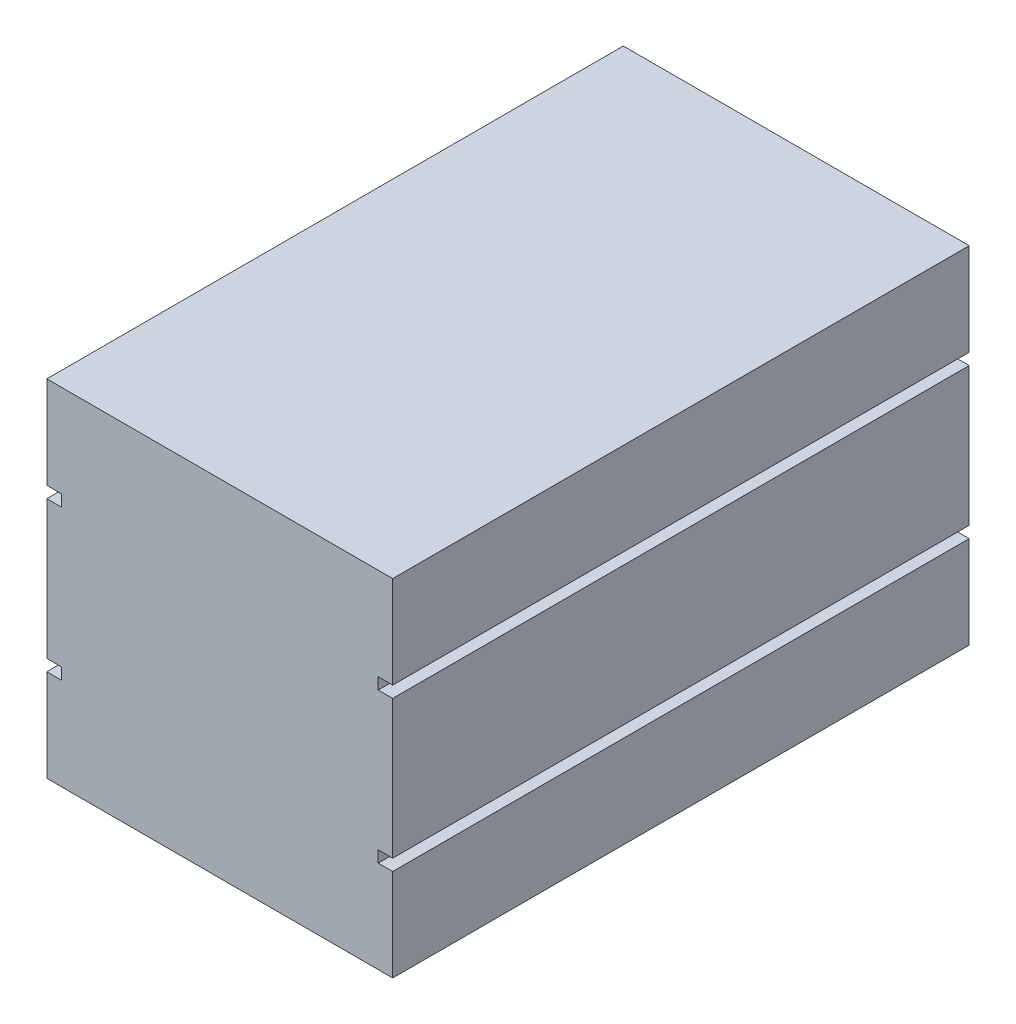
SolidWorks part; units mm, degrees
ref_plane "Front Plane" through (0, 0, 0) normal (0, 0, 1) x (1, 0, 0)
ref_plane "Top Plane" through (0, 0, 0) normal (0, 1, 0) x (1, 0, 0)
ref_plane "Right Plane" through (0, 0, 0) normal (1, 0, 0) x (0, 0, -1)
sketch "Sketch1" plane through (0, 0, 0) normal (1, 0, 0) x (0, 0, -1)
  line L1 (-25, -15) -> (25, -15)
  line L2 (-25, -15) -> (-25, 15)
  line L3 (-25, 15) -> (25, 15)
  line L4 (25, -15) -> (25, 15)
  line L5 (-25, -15) -> (25, 15) construction
  line L6 (-25, 15) -> (25, -15) construction
  point P0 (0, 0)
  dimension "D1" = 50
  dimension "D2" = 30
extrude "Boss-Extrude1" add sketch "Sketch1" along normal blind 30
sketch "Sketch3" plane through (0, 0, -25) normal (0, 0, -1) x (-1, 0, 0)
  line L0 (-30, -15) -> (-30, 15) construction
  circle A0 centre (-15, 0) radius 5.9333
  point P2 (-30, 0)
  dimension "D1" = 15
extrude "Cut-Extrude1" cut sketch "Sketch3" against normal blind 40
sketch "Sketch4" plane through (0, 0, -25) normal (0, 0, -1) x (-1, 0, 0)
  line L0 (-30, -15) -> (-30, 15) construction
  line L1 (-30, 7) -> (-28.745, 7)
  line L2 (-30, 7) -> (-30, 6)
  line L3 (-30, 6) -> (-28.745, 6)
  line L4 (-28.745, 7) -> (-28.745, 6)
  line L5 (-30, 15) -> (0, 15) construction
  line L6 (-30, -6) -> (-28.745, -6)
  line L7 (-30, -6) -> (-30, -7)
  line L8 (-30, -7) -> (-28.745, -7)
  line L9 (-28.745, -6) -> (-28.745, -7)
  line L10 (-30, -15) -> (0, -15) construction
  line L11 (-15, 15) -> (-15, -15) construction
  line L12 (-1.255, -6) -> (-1.255, -7)
  line L13 (0, -7) -> (-1.255, -7)
  line L14 (0, -6) -> (-1.255, -6)
  line L15 (0, -6) -> (0, -7)
  line L16 (0, 7) -> (0, 6)
  line L17 (0, 6) -> (-1.255, 6)
  line L18 (-1.255, 7) -> (-1.255, 6)
  line L19 (0, 7) -> (-1.255, 7)
  dimension "D1" = 1
  dimension "D2" = 1
  dimension "D3" = 8
  dimension "D4" = 8
extrude "Cut-Extrude2" cut sketch "Sketch4" against normal through all
